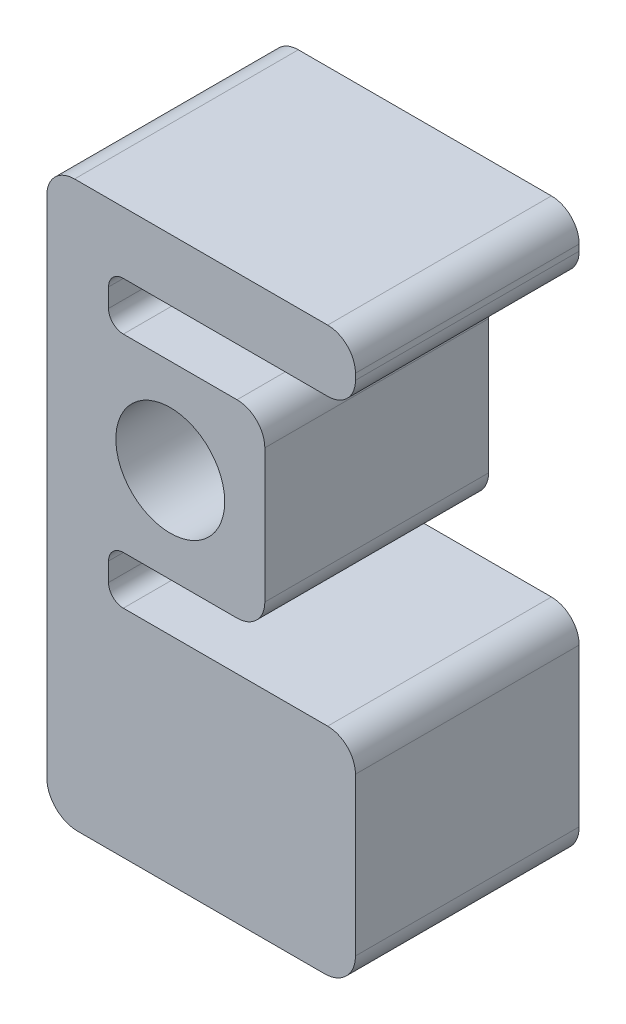
SolidWorks part; units mm, degrees
material "Pink Foam"
ref_plane "Front Plane" through (0, 0, 0) normal (0, 0, 1) x (1, 0, 0)
ref_plane "Top Plane" through (0, 0, 0) normal (0, 1, 0) x (1, 0, 0)
ref_plane "Right Plane" through (0, 0, 0) normal (1, 0, 0) x (0, 0, -1)
sketch "Sketch1" plane through (0, 0, 0) normal (0, 0, 1) x (1, 0, 0)
  line L0 (-25.4, -67.48) -> (-25.4, 36.365)
  line L2 (38.1, -67.48) -> (38.1, -35.095)
  line L3 (32.385, -29.38) -> (-9.652, -29.38)
  line L4 (-12.7, -26.332) -> (-12.7, -22.503)
  line L5 (-9.652, -19.455) -> (0, -19.455)
  line L6 (-9.652, 19.455) -> (0, 19.455)
  line L7 (-12.7, 22.503) -> (-12.7, 26.332)
  line L8 (-9.652, 29.38) -> (32.385, 29.38)
  line L9 (38.1, 35.095) -> (38.1, 36.365)
  line L10 (32.385, 42.08) -> (-19.685, 42.08)
  line L15 (0, -11.2) -> (0, -19.455) construction
  line L16 (0, 11.2) -> (0, 19.455) construction
  line L17 (11.2, 0) -> (19.455, 0) construction
  line L18 (0, 19.455) -> (13.74, 19.455)
  line L19 (19.455, 13.74) -> (19.455, 0)
  line L20 (19.455, 0) -> (19.455, -13.74)
  line L21 (13.74, -19.455) -> (0, -19.455)
  line L24 (31.75, -73.83) -> (-19.05, -73.83)
  circle A0 centre (0, 0) radius 11.2
  arc A3 (-19.685, 42.08) -> (-25.4, 36.365) centre (-19.685, 36.365) ccw
  arc A4 (38.1, 36.365) -> (32.385, 42.08) centre (32.385, 36.365) ccw
  arc A6 (32.385, 29.38) -> (38.1, 35.095) centre (32.385, 35.095) ccw
  arc A7 (38.1, -35.095) -> (32.385, -29.38) centre (32.385, -35.095) ccw
  arc A8 (19.455, -13.74) -> (13.74, -19.455) centre (13.74, -13.74) cw
  arc A9 (13.74, 19.455) -> (19.455, 13.74) centre (13.74, 13.74) cw
  arc A10 (-12.7, 26.332) -> (-9.652, 29.38) centre (-9.652, 26.332) cw
  arc A11 (-9.652, 19.455) -> (-12.7, 22.503) centre (-9.652, 22.503) cw
  arc A12 (-12.7, -22.503) -> (-9.652, -19.455) centre (-9.652, -22.503) cw
  arc A13 (-9.652, -29.38) -> (-12.7, -26.332) centre (-9.652, -26.332) cw
  arc A14 (31.75, -73.83) -> (38.1, -67.48) centre (31.75, -67.48) ccw
  arc A15 (-19.05, -73.83) -> (-25.4, -67.48) centre (-19.05, -67.48) cw
  point P12 (0, 11.2)
  point P20 (0, -11.2)
  point P22 (11.2, 0)
  point P45 (-12.7, 29.38)
  point P48 (-12.7, 19.455)
  point P53 (-12.7, -29.38)
  point P57 (38.1, -73.83)
  point P60 (38.1, -73.83)
  point P63 (-25.4, -73.83)
  dimension "D1" = 22.4
  dimension "D11" = 3.048
  dimension "D9" = 5.715
  dimension "D14" = 5.715
  dimension "D12" = 6.35
  dimension "D2" = 25.4
  dimension "D3" = 8.255
  dimension "D4" = 9.925
  dimension "D5" = 44.45
  dimension "D6" = 9.925
  dimension "D7" = 12.7
  dimension "D8" = 12.7
  dimension "D10" = 63.5
extrude "Boss-Extrude1" add sketch "Sketch1" along normal blind 46.0375
